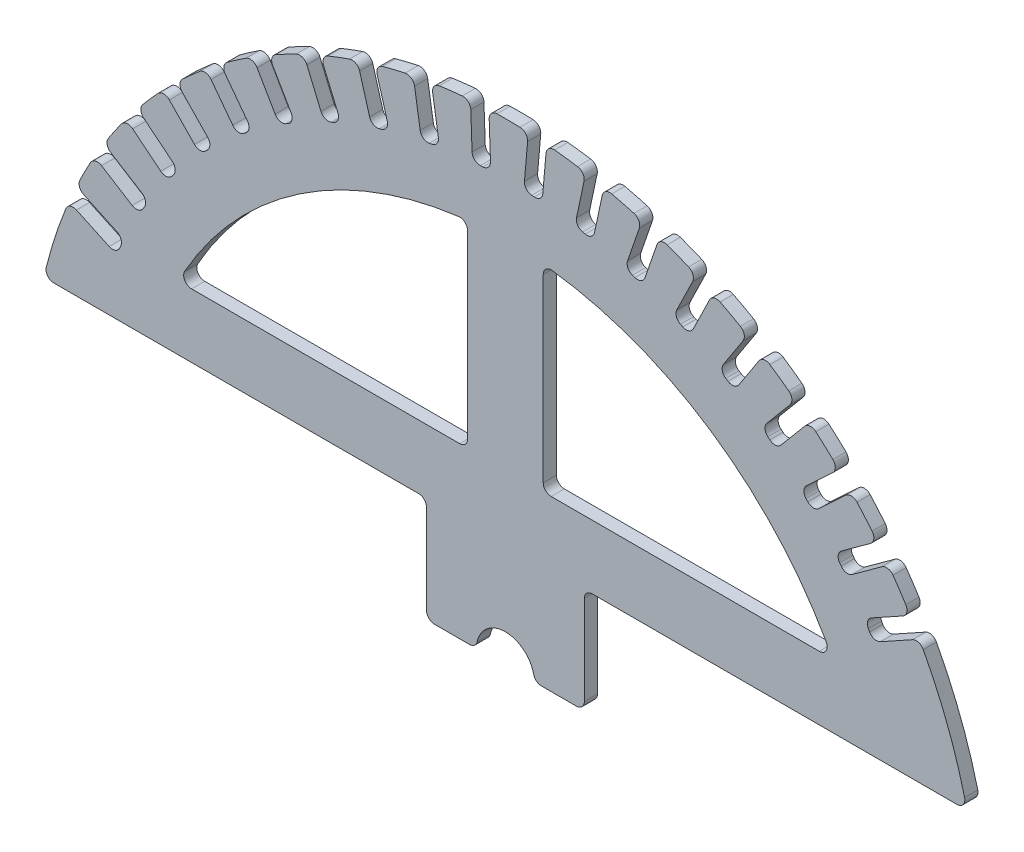
SolidWorks part; units mm, degrees
ref_plane "Plan de face" through (0, 0, 0) normal (0, 0, 1) x (1, 0, 0)
ref_plane "Plan de dessus" through (0, 0, 0) normal (0, 1, 0) x (1, 0, 0)
ref_plane "Plan de droite" through (0, 0, 0) normal (1, 0, 0) x (0, 0, -1)
sketch "Esquisse1" plane through (0, 0, 0) normal (0, 0, 1) x (1, 0, 0)
  line L0 (-11, 0) -> (-30, 0)
  line L2 (0, 0) -> (0, 12.5) construction
  line L3 (30, 40) -> (175.4993, 40)
  line L4 (30, 40) -> (30, 0)
  line L5 (30, 0) -> (11, 0)
  line L6 (-30, 40) -> (-30, 0)
  line L7 (-175.4993, 40) -> (-30, 40)
  arc A0 (-175.4993, 40) -> (175.4993, 40) centre (0, 0) cw
  arc A1 (11, 0) -> (-11, 0) centre (0, 0) ccw
extrude "Boss.-Extru.1" add sketch "Esquisse1" along normal blind 5
sketch "Esquisse2" plane through (0, 0, 5) normal (0, 0, 1) x (1, 0, 0)
  line L0 (-113.1371, 40) -> (-113.1371, 140)
  line L2 (-113.1371, 140) -> (-135, 140)
  line L3 (-135, 140) -> (-135, 40)
  line L4 (-175.4993, 40) -> (-30, 40) construction
  line L5 (-113.1371, 40) -> (-135, 40)
  arc A0 (175.4993, 40) -> (-175.4993, 40) centre (0, 0) ccw construction
  dimension "D1" = 100
  dimension "D2" = 21.8629
extrude "Enlèv. mat.-Extru.1" [suppressed] cut sketch "Esquisse2" against normal through all
sketch "Esquisse3" plane through (0, 0, 5) normal (0, 0, 1) x (1, 0, 0)
  line L0 (0, 0) -> (-163.1354, 76.0713) construction
  line L1 (-163.1354, 76.0713) -> (-145.0092, 67.6189)
  line L2 (-145.0092, 67.6189) -> (-147.9676, 61.2748)
  line L3 (-147.9676, 61.2748) -> (-165.9703, 69.6696)
  line L4 (-175.4993, 40) -> (-30, 40) construction
  arc A0 (175.4993, 40) -> (-175.4993, 40) centre (0, 0) ccw construction
  arc A1 (-165.9703, 69.6696) -> (-163.1354, 76.0713) centre (-41.1564, 18.2257) cw
  dimension "D1" = 7
  dimension "D2" = 20
  dimension "D3" = 25
extrude "Enlèv. mat.-Extru.2" cut sketch "Esquisse3" against normal through all
fillet "Congé1" radius 3 4 edges at (-145.0092, 67.6189, 2.5) (-163.1354, 76.0713, 2.5) (-165.9703, 69.6696, 2.5) (-147.9676, 61.2748, 2.5)
pattern_circular "Répétition circulaire1" count 19 every 7 about axis through (0, 0, 0) along (0, 0, 1) of "Enlèv. mat.-Extru.2", "Congé1"
fillet "Congé2" [suppressed] radius 40
fillet "Congé3" [suppressed] radius 10
sketch "Esquisse4" plane through (0, 0, 0) normal (0, 0, -1) x (-1, 0, 0)
  line L0 (-124.3814, 64.2594) -> (-14.3814, 64.2594)
  line L1 (-14.3814, 64.2594) -> (-14.3814, 139.2594)
  line L3 (-30, 40) -> (-175.4993, 40) construction
  arc A0 (-124.3814, 64.2594) -> (-14.3814, 139.2594) centre (0, 0) cw
  dimension "D1" = 140
  dimension "D2" = 24.2594
  dimension "D3" = 14.3814
  dimension "D4" = 75
  dimension "D5" = 110
extrude "Enlèv. mat.-Extru.3" cut sketch "Esquisse4" against normal blind 10
fillet "Congé4" radius 3 3 edges at (14.3814, 139.2594, 2.5) (14.3814, 64.2594, 2.5) (124.3814, 64.2594, 2.5)
mirror "Symétrie1" about plane through (0, 0, 0) normal (1, 0, 0) of "Congé4", "Enlèv. mat.-Extru.3"
fillet "Congé5" radius 3 8 edges at (-175.4993, 40, 2.5) (-30, 40, 2.5) (-30, 0, 2.5) (11, 0, 2.5) (-11, 0, 2.5) (30, 0, 2.5) (30, 40, 2.5) (175.4993, 40, 2.5)
equation "\"D4@Esquisse1\"=\"D3@Esquisse1\"/2"
